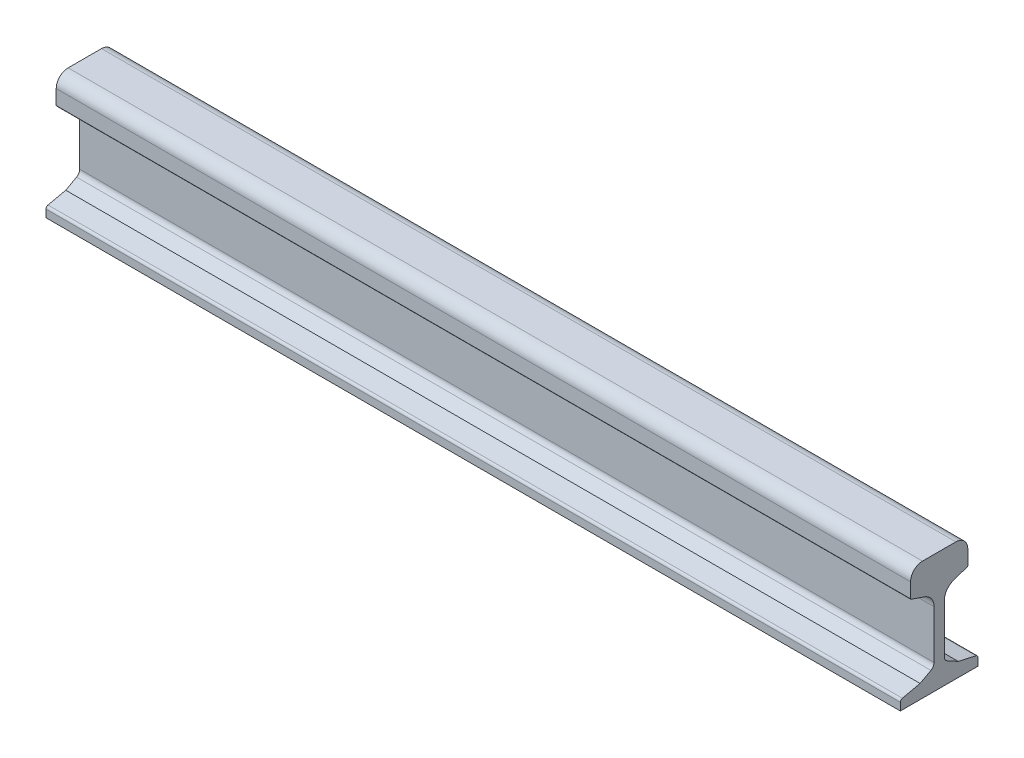
SolidWorks part; units mm, degrees
material "1.0503 (C45)"
ref_plane "Ebene vorne" through (0, 0, 0) normal (0, 0, 1) x (1, 0, 0)
ref_plane "Ebene oben" through (0, 0, 0) normal (0, 1, 0) x (1, 0, 0)
ref_plane "Ebene rechts" through (0, 0, 0) normal (1, 0, 0) x (0, 0, -1)
sketch "Skizze1" plane through (0, 0, 0) normal (1, 0, 0) x (0, 0, -1)
  line L0 (-45.4567, -1.0135) -> (45.4567, -1.0135)
  line L1 (45.4567, -1.0135) -> (45.4567, 7.8288)
  line L2 (43.1115, 10.7565) -> (22.3648, 15.396)
  line L3 (22.3648, 15.396) -> (9.6582, 22.2998)
  line L4 (6, 28.4506) -> (6, 85.0363)
  line L5 (17.6378, 100.7036) -> (32.8258, 105.9377)
  line L6 (33.5, 106.8831) -> (33.5, 124)
  line L7 (19.5, 138) -> (-19.5, 138)
  line L8 (0, 0) -> (0, 138) construction
  line L9 (-45.4567, -1.0135) -> (-45.4567, 7.8288)
  line L10 (-43.1115, 10.7565) -> (-22.3648, 15.396)
  line L11 (-22.3648, 15.396) -> (-9.6582, 22.2998)
  line L12 (-6, 28.4506) -> (-6, 85.0363)
  line L13 (-17.6378, 100.7036) -> (-32.8258, 105.9377)
  line L14 (-33.5, 106.8831) -> (-33.5, 124)
  arc A0 (6, 85.0363) -> (17.6378, 100.7036) centre (22.3648, 85.0363) cw
  arc A1 (-6, 85.0363) -> (-17.6378, 100.7036) centre (-22.3648, 85.0363) ccw
  arc A2 (-33.5, 124) -> (-19.5, 138) centre (-19.5, 124) cw
  arc A3 (33.5, 124) -> (19.5, 138) centre (19.5, 124) ccw
  arc A4 (9.6582, 22.2998) -> (6, 28.4506) centre (13, 28.4506) cw
  arc A5 (-9.6582, 22.2998) -> (-6, 28.4506) centre (-13, 28.4506) ccw
  arc A6 (-45.4567, 7.8288) -> (-43.1115, 10.7565) centre (-42.4567, 7.8288) cw
  arc A7 (45.4567, 7.8288) -> (43.1115, 10.7565) centre (42.4567, 7.8288) ccw
  arc A8 (-32.8258, 105.9377) -> (-33.5, 106.8831) centre (-32.5, 106.8831) cw
  arc A9 (32.8258, 105.9377) -> (33.5, 106.8831) centre (32.5, 106.8831) ccw
  point P22 (-33.5, 138)
  point P25 (33.5, 138)
  point P30 (6, 24.2874)
  point P33 (-6, 24.2874)
  point P36 (-45.4567, 10.232)
  point P39 (45.4567, 10.232)
  point P40 (0, 27.5473)
  point P44 (33.5, 106.17)
  dimension "D1" = 16.3648
  dimension "D5" = 14
  dimension "D7" = 7
  dimension "D8" = 3
  dimension "D10" = 1
  dimension "D2" = 67
  dimension "D3" = 138
  dimension "D4" = 31.83
  dimension "D6" = 12
  dimension "D9" = 11.77
  dimension "D11" = 101.7171
  dimension "D12" = 86.0499
  dimension "D13" = 9.6582
  dimension "D14" = 32.8258
  dimension "D15" = 42.4567
  dimension "D16" = 43.1115
extrude "Aufsatz-Linear austragen1" add sketch "Skizze1" along normal mid plane 1000
